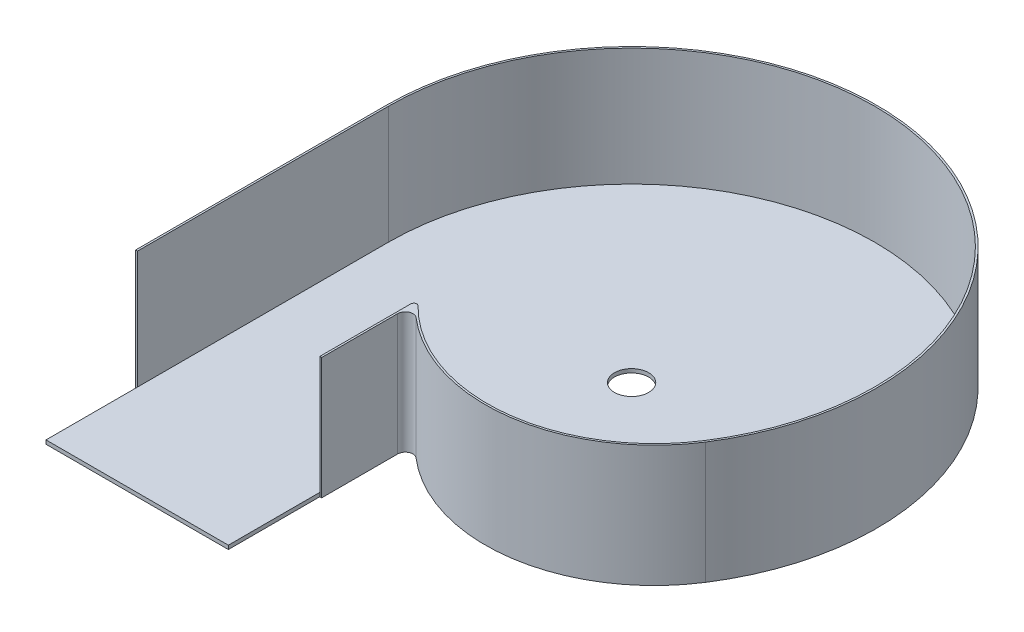
SolidWorks part; units mm, degrees
ref_plane "Front Plane" through (0, 0, 0) normal (0, 0, 1) x (1, 0, 0)
ref_plane "Top Plane" through (0, 0, 0) normal (0, 1, 0) x (1, 0, 0)
ref_plane "Right Plane" through (0, 0, 0) normal (1, 0, 0) x (0, 0, -1)
sketch "Sketch1" plane through (0, 0, 0) normal (0, 1, 0) x (1, 0, 0)
  line L0 (-203.2, 0) -> (-203.2, -209.7483)
  line L2 (-50.8, -209.7483) -> (-50.8, -196.7476)
  line L4 (-204.7875, 0) -> (-204.7875, -209.7483)
  line L5 (-50.8, -196.7476) -> (-50.8, -133.7917)
  line L7 (-50.8, -209.7483) -> (-50.8, -196.7476) construction
  line L9 (-204.7875, -209.7483) -> (-203.2, -209.7483)
  line L10 (-49.2125, -209.7483) -> (-50.8, -209.7483)
  line L11 (-49.2125, -209.7483) -> (-49.2125, -198.7864) construction
  line L13 (-49.2125, -146.2483) -> (-49.2125, -209.7483)
  arc A0 (-49.2125, -197.1506) -> (147.6582, -139.5969) centre (0, 0) ccw construction
  arc A1 (172.2844, -110.7069) -> (-204.7875, 0) centre (0, 0) ccw
  arc A2 (-50.8, -196.7476) -> (-203.2, 0) centre (0, 0) ccw construction
  arc A3 (-46.4443, -132.0156) -> (170.9489, -109.8487) centre (53.4215, -34.3277) ccw
  arc A4 (-38.7213, -141.4345) -> (172.2844, -110.7069) centre (53.4215, -34.3277) ccw
  arc A5 (-59.4191, -119.3521) -> (172.2844, -110.7069) centre (53.4215, -34.3277) ccw construction
  arc A6 (170.9489, -109.8487) -> (-203.2, 0) centre (0, 0) ccw
  arc A7 (-49.2125, -146.2483) -> (-38.7213, -141.4345) centre (-42.8625, -146.2483) cw
  arc A9 (-58.1513, -118.3968) -> (170.9489, -109.8487) centre (53.4215, -34.3277) ccw construction
  arc A10 (-49.2125, -198.7864) -> (-204.7875, 0) centre (0, 0) ccw construction
  arc A11 (-46.4443, -132.0156) -> (-50.8, -133.7917) centre (-48.26, -133.7917) ccw
  point P1 (-48.6974, -197.2824)
  point P14 (0, 0)
  point P15 (-50.8, -121.5045)
  dimension "D1" = 406.4
  dimension "D5" = 152.4
  dimension "D6" = 1.5875
  dimension "D7" = 6.35
  dimension "D8" = 139.7
  dimension "D9" = 2.54
  dimension "D2" = 152.4
  dimension "D3" = 63.5
  dimension "D4" = 1.5875
extrude "Boss-Extrude1" add sketch "Sketch1" along normal blind 101.6
sketch "Sketch2" plane through (0, 0, 0) normal (0, 1, 0) x (1, 0, 0)
  line L0 (-50.8, -133.7917) -> (-50.8, -209.7483) construction
  line L1 (-203.2, -209.7483) -> (-203.2, 0) construction
  line L2 (-50.8, -133.7917) -> (-50.8, -286.1917)
  line L3 (-203.2, -286.1917) -> (-203.2, 0)
  line L4 (-203.2, -286.1917) -> (-50.8, -286.1917)
  arc A0 (170.9489, -109.8487) -> (-203.2, 0) centre (0, 0) ccw construction
  arc A1 (-46.4443, -132.0156) -> (-50.8, -133.7917) centre (-48.26, -133.7917) ccw construction
  arc A2 (-46.4443, -132.0156) -> (170.9489, -109.8487) centre (53.4215, -34.3277) ccw construction
  arc A3 (170.9489, -109.8487) -> (-203.2, 0) centre (0, 0) ccw
  arc A4 (-46.4443, -132.0156) -> (-50.8, -133.7917) centre (-48.26, -133.7917) ccw
  arc A5 (-46.4443, -132.0156) -> (170.9489, -109.8487) centre (53.4215, -34.3277) ccw
  dimension "D1" = 152.4
extrude "Boss-Extrude2" add sketch "Sketch2" along normal blind 3.175
sketch "Sketch3" plane through (0, 3.175, 0) normal (0, 1, 0) x (1, 0, 0)
  circle A0 centre (0, 0) radius 14.2875
  dimension "D1" = 28.575
extrude "Cut-Extrude1" cut sketch "Sketch3" against normal through all
